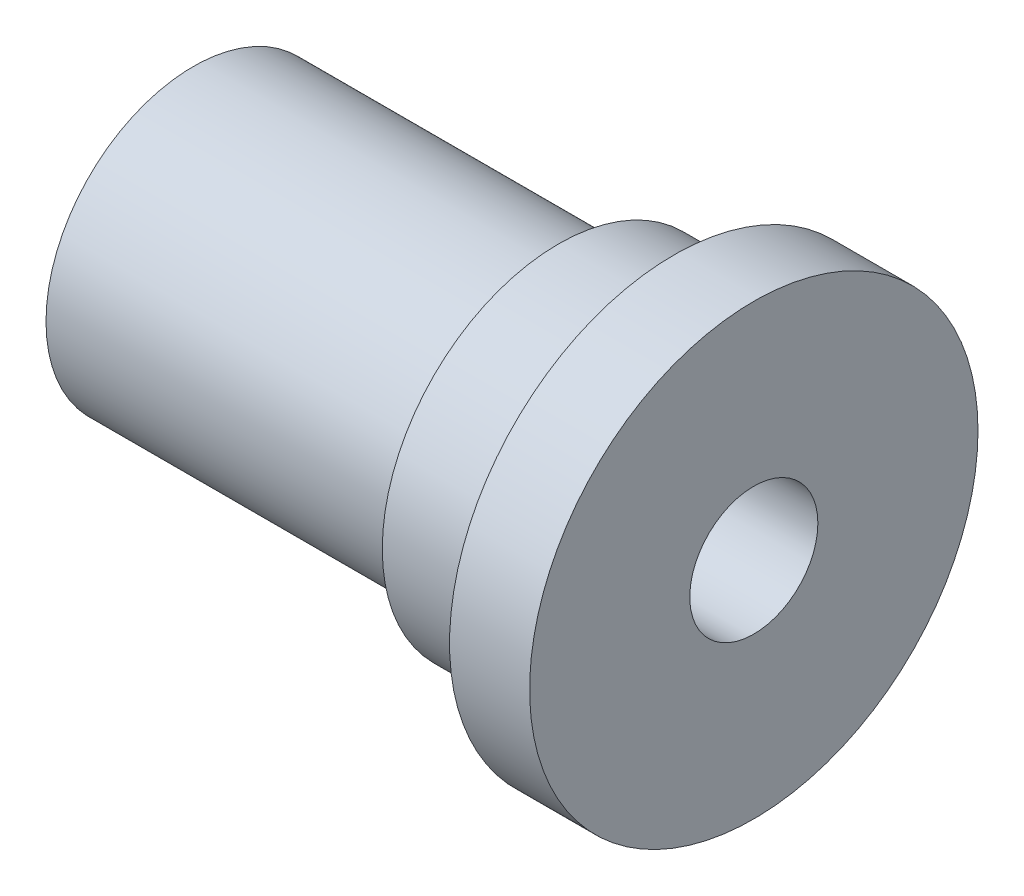
SolidWorks part; units mm, degrees
material "PA Type 6"
ref_plane "Front Plane" through (0, 0, 0) normal (0, 0, 1) x (1, 0, 0)
ref_plane "Top Plane" through (0, 0, 0) normal (0, 1, 0) x (1, 0, 0)
ref_plane "Right Plane" through (0, 0, 0) normal (1, 0, 0) x (0, 0, -1)
sketch "Sketch1" plane through (0, 0, 0) normal (0, 1, 0) x (1, 0, 0)
  line L0 (-18, 0) -> (-30, 0) construction
  line L1 (0, 0) -> (0, 11) construction
  line L2 (0, 11) -> (-7.2, 11)
  line L3 (-7.2, 11) -> (-7.2, 9.2)
  line L4 (-7.2, 9.2) -> (-30, 9.2)
  line L5 (-30, 9.2) -> (-30, 0)
  line L6 (-18, 0) -> (-30, 0)
  line L7 (0, 4) -> (-18, 4)
  line L8 (-18, 4) -> (-18, 0)
  line L9 (0, 11) -> (0, 14)
  line L10 (0, 14) -> (5, 14)
  line L11 (5, 14) -> (5, 4)
  line L12 (5, 4) -> (0, 4)
  line L13 (-30, 0) -> (2, 0) construction
  dimension "D1" = 7.2
  dimension "D2" = 30
  dimension "D3" = 11
  dimension "D4" = 9.2
  dimension "D5" = 4
  dimension "D6" = 18
  dimension "D7" = 3
  dimension "D8" = 5
revolve "Revolve1" add sketch "Sketch1" angle 360 about L0
sketch "Sketch3" plane through (0, 0, 0) normal (0, 1, 0) x (1, 0, 0)
  line L0 (0, 0) -> (-11, 0) construction
  circle A0 centre (-11, 0) radius 2.5
  dimension "D1" = 11
extrude "Cut-Extrude1" cut sketch "Sketch3" against normal blind 10
